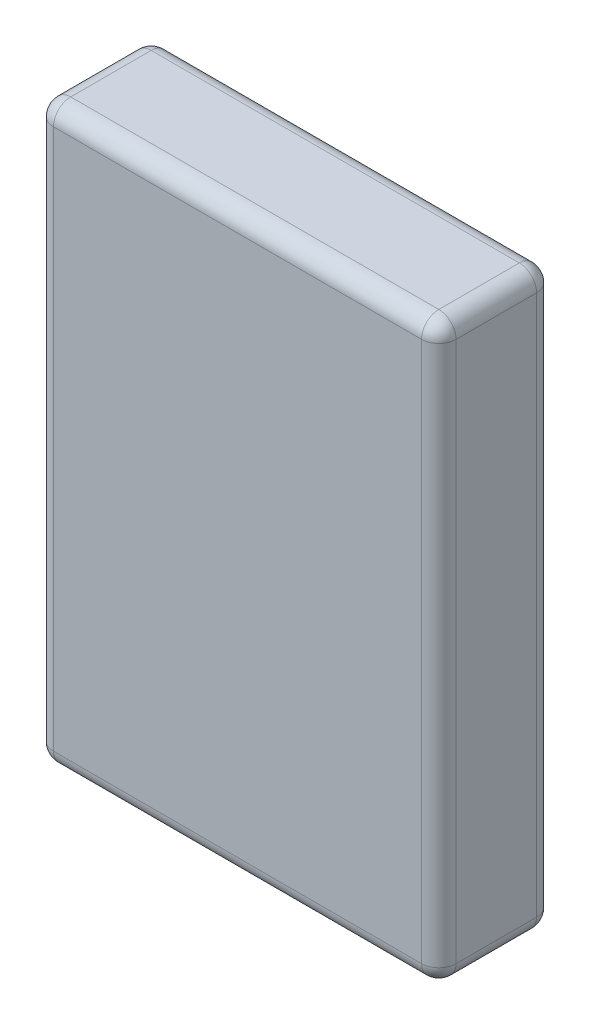
SolidWorks part; units mm, degrees
ref_plane "Front Plane" through (0, 0, 0) normal (0, 0, 1) x (1, 0, 0)
ref_plane "Top Plane" through (0, 0, 0) normal (0, 1, 0) x (1, 0, 0)
ref_plane "Right Plane" through (0, 0, 0) normal (1, 0, 0) x (0, 0, -1)
sketch "Sketch1" plane through (0, 0, 0) normal (0, 0, 1) x (1, 0, 0)
  line L1 (0, 0) -> (70, 0)
  line L2 (0, 0) -> (0, 100)
  line L3 (0, 100) -> (70, 100)
  line L4 (70, 0) -> (70, 100)
  dimension "D1" = 70
  dimension "D2" = 100
extrude "Boss-Extrude1" add sketch "Sketch1" along normal blind 20
fillet "Fillet1" radius 3 12 edges at (35, 0, 0) (70, 50, 0) (35, 100, 0) (0, 50, 0) (35, 100, 20) (70, 50, 20) (35, 0, 20) (0, 50, 20) (0, 100, 10) (70, 100, 10) (0, 0, 10) (70, 0, 10)
